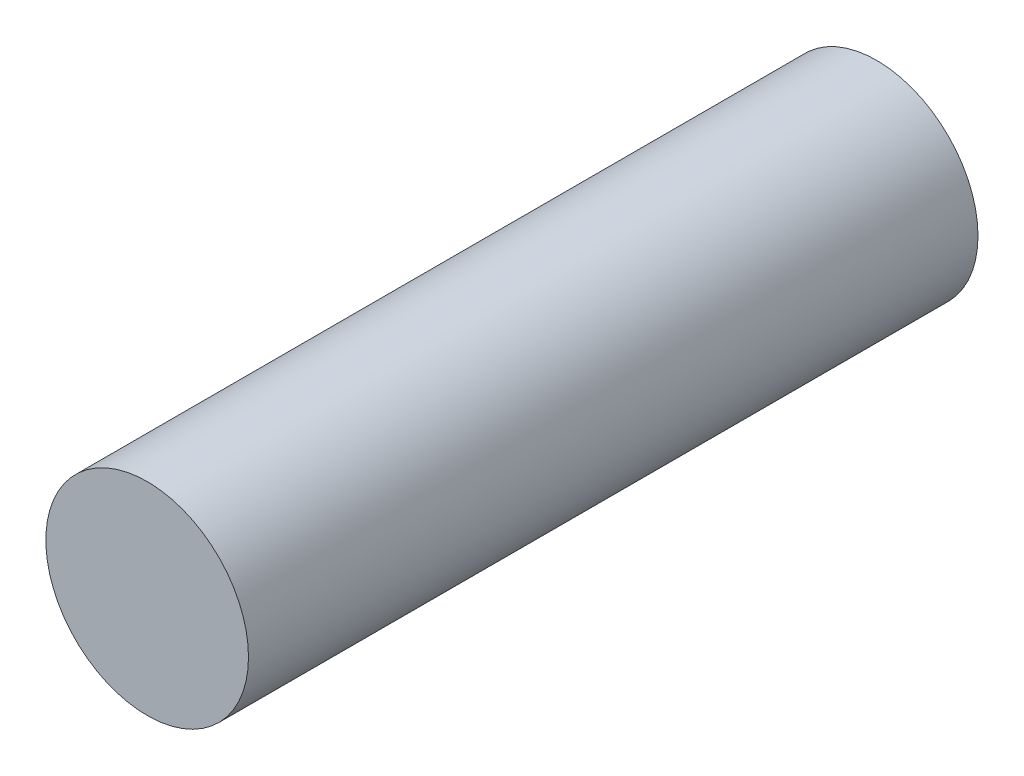
SolidWorks part; units mm, degrees
material "PBT General Purpose"
ref_plane "Front Plane" through (0, 0, 0) normal (0, 0, 1) x (1, 0, 0)
ref_plane "Top Plane" through (0, 0, 0) normal (0, 1, 0) x (1, 0, 0)
ref_plane "Right Plane" through (0, 0, 0) normal (1, 0, 0) x (0, 0, -1)
sketch "Sketch3" plane through (0, 0, 0) normal (0, 0, 1) x (1, 0, 0)
  circle A0 centre (0, 0) radius 1.25
  dimension "D1" = 2.5
extrude "Boss-Extrude1" add sketch "Sketch3" along normal blind 9
